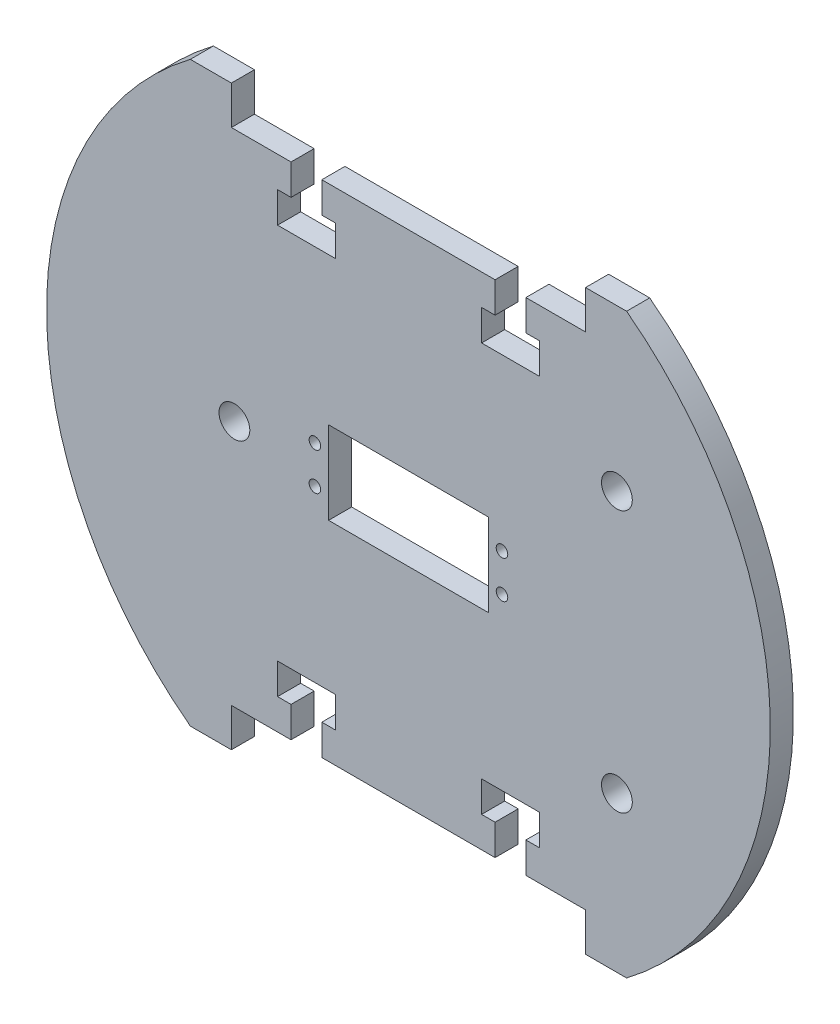
SolidWorks part; units mm, degrees
ref_plane "Front Plane" through (0, 0, 0) normal (0, 0, 1) x (1, 0, 0)
ref_plane "Top Plane" through (0, 0, 0) normal (0, 1, 0) x (1, 0, 0)
ref_plane "Right Plane" through (0, 0, 0) normal (1, 0, 0) x (0, 0, -1)
sketch "Sketch8" plane through (0, 0, 0) normal (0, 0, 1) x (1, 0, 0)
  line L46 (-56.6657, -75) -> (-46, -75)
  line L47 (-30.5, -65) -> (-30.5, -57.0293)
  line L48 (30.5, -57.0293) -> (30.5, -65)
  line L49 (-46, -65) -> (-30.5, -65)
  line L50 (46, -65) -> (46, -75)
  line L52 (-34, 49.0293) -> (-34, 57.0293)
  line L53 (19, -57.0293) -> (19, -49.0293)
  line L54 (-22.5, 65) -> (-22.5, 57.0293)
  line L55 (-30.5, 57.0293) -> (-30.5, 65)
  line L56 (-30.5, 65) -> (-46, 65)
  line L57 (56.6657, 75) -> (46, 75)
  line L58 (-22.5, -57.0293) -> (-22.5, -65)
  line L59 (-46, 65) -> (-46, 75)
  line L60 (30.5, -65) -> (46, -65)
  line L61 (19, 57.0293) -> (22.5, 57.0293)
  line L62 (-34, -57.0293) -> (-34, -49.0293)
  line L63 (34, 49.0293) -> (19, 49.0293)
  line L64 (-19, 49.0293) -> (-34, 49.0293)
  line L65 (34, -49.0293) -> (34, -57.0293)
  line L66 (46, 75) -> (46, 65)
  line L67 (34, 57.0293) -> (34, 49.0293)
  line L68 (-22.5, -65) -> (22.5, -65)
  line L70 (-46, -75) -> (-46, -65)
  line L71 (22.5, -65) -> (22.5, -57.0293)
  line L72 (19, -49.0293) -> (34, -49.0293)
  line L73 (-34, -49.0293) -> (-19, -49.0293)
  line L74 (-46, 75) -> (-56.6657, 75)
  line L75 (-19, -49.0293) -> (-19, -57.0293)
  line L76 (34, -57.0293) -> (30.5, -57.0293)
  line L77 (22.5, 57.0293) -> (22.5, 65)
  line L78 (46, 65) -> (30.5, 65)
  line L80 (22.5, 65) -> (-22.5, 65)
  line L81 (-22.5, 57.0293) -> (-19, 57.0293)
  line L82 (22.5, -57.0293) -> (19, -57.0293)
  line L83 (30.5, 65) -> (30.5, 57.0293)
  line L84 (30.5, 57.0293) -> (34, 57.0293)
  line L85 (-19, 57.0293) -> (-19, 49.0293)
  line L86 (-30.5, -57.0293) -> (-34, -57.0293)
  line L87 (46, -75) -> (56.6657, -75)
  line L88 (19, 49.0293) -> (19, 57.0293)
  line L90 (-34, 57.0293) -> (-30.5, 57.0293)
  line L91 (-19, -57.0293) -> (-22.5, -57.0293)
  line L92 (-125.2624, 0) -> (139.2989, 0) construction
  line L93 (0, 88.7884) -> (0, -98.0596) construction
  line L94 (124.3842, 0) -> (260.3146, 0) construction
  line L95 (0, 88.5153) -> (0, -14.7198) construction
  line L96 (-20.75, -10.75) -> (20.75, -10.75)
  line L97 (-20.75, 10.75) -> (-20.75, -10.75)
  line L98 (20.75, 10.75) -> (-20.75, 10.75)
  line L99 (20.75, -10.75) -> (20.75, 10.75)
  arc A10 (-56.6657, 75) -> (-56.6657, -75) centre (0, 0) ccw
  arc A12 (56.6657, -75) -> (56.6657, 75) centre (0, 0) ccw
  circle A14 centre (-24.3, -4.875) radius 1.5
  circle A15 centre (-24.3, 4.875) radius 1.5
  circle A16 centre (24.3, 4.875) radius 1.5
  circle A17 centre (24.3, -4.875) radius 1.5
  point P20 (94, 0)
  point P21 (-94, 0)
  point P22 (0, 0)
  point P23 (0, 0)
  point P31 (-73.7821, -11.4506)
  dimension "D1" = 94
  dimension "D19" = 3
  dimension "D2" = 150
  dimension "D3" = 10
  dimension "D4" = 7.9707
  dimension "D5" = 8
  dimension "D6" = 15
  dimension "D10" = 94
  dimension "D11" = 46
  dimension "D12" = 34
  dimension "D13" = 49.0293
  dimension "D17" = 41.5
  dimension "D18" = 21.5
  dimension "D20" = 48.6
  dimension "D21" = 9.75
  dimension "D22" = 5.875
  dimension "D23" = 5.875
  dimension "D24" = 9.75
  dimension "D25" = 3.55
  dimension "D26" = 3.55
  dimension "D27" = 5.875
  dimension "D28" = 94
extrude "Boss-Extrude1" add sketch "Sketch8" along normal blind 6
sketch "Sketch10" plane through (0, 0, 6) normal (0, 0, 1) x (1, 0, 0)
  line L0 (0, 84.1737) -> (0, -84.1737) construction
  line L1 (8.82, -0.723) -> (-10.8022, 18.8992) construction
  line L2 (8.82, -0.723) -> (-10.8022, -20.3452) construction
  line L3 (8.82, -0.723) -> (36.57, -0.723) construction
  line L4 (-10.8022, 18.8992) -> (-10.8022, -20.3452) construction
  line L5 (-28.5032, 38.5215) -> (-28.5032, -39.9674) construction
  line L6 (-45.2176, -0.723) -> (62.8576, -0.723) construction
  line L7 (8.82, 35.4092) -> (8.82, -36.8551) construction
  line L8 (8.82, -0.723) -> (62.9786, -0.723) construction
  line L9 (8.82, 71.5413) -> (8.82, -72.9873) construction
  line L10 (-99.2551, -0.723) -> (116.8951, -0.723) construction
  line L11 (8.82, -0.723) -> (-28.5032, -39.9674) construction
  line L12 (8.82, -0.723) -> (-28.5032, 38.5215) construction
  circle A0 centre (54.15, -34.723) radius 4
  circle A1 centre (54.15, 33.277) radius 4
  circle A2 centre (-45.21, -0.723) radius 4
  point P0 (0, 0)
  point P4 (0, 0)
  point P7 (8.82, -0.723)
  point P20 (8.82, -0.723)
  point P23 (8.82, -0.723)
  point P31 (8.82, -0.723)
  dimension "D8" = 8
  dimension "D1" = 27.75
  dimension "D2" = 90
  dimension "D3" = 34
  dimension "D4" = 34
  dimension "D5" = 99.36
  dimension "D6" = 99.36
  dimension "D7" = 54.03
  dimension "D9" = 54.03
  dimension "D10" = 8.82
extrude "Cut-Extrude2" cut sketch "Sketch10" against normal through all both and the other way through all
